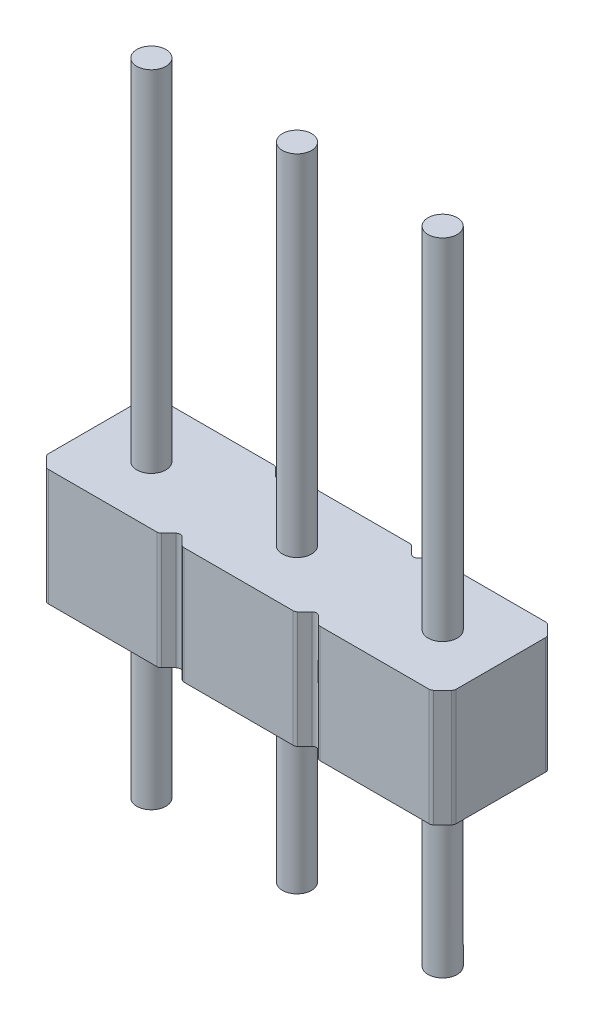
SolidWorks part; units mm, degrees
ref_plane "Ön Düzlem" through (0, 0, 0) normal (0, 0, 1) x (1, 0, 0)
ref_plane "Üst Düzlem" through (0, 0, 0) normal (0, 1, 0) x (1, 0, 0)
ref_plane "Sağ Düzlem" through (0, 0, 0) normal (1, 0, 0) x (0, 0, -1)
sketch "Çizim1" plane through (0, 0, 0) normal (0, 1, 0) x (1, 0, 0)
  line L0 (-3.5, 0) -> (0, 0) construction
  line L1 (0, 0) -> (0, 1) construction
  line L2 (-3.4777, 0.8223) -> (-3.3223, 0.9777)
  line L3 (-3.2684, -1) -> (-1.4016, -1)
  line L4 (-3.5, -0.7684) -> (-3.5, 0.7684)
  line L5 (-3.2684, 1) -> (-1.4016, 1)
  line L6 (3.5, -0.7684) -> (3.5, 0.7684)
  line L7 (-3.5, -1) -> (3.5, 1) construction
  line L8 (-3.5, 1) -> (3.5, -1) construction
  line L9 (-3.4777, -0.8223) -> (-3.3223, -0.9777)
  line L10 (3.3223, 0.9777) -> (3.4777, 0.8223)
  line L11 (3.3223, -0.9777) -> (3.4777, -0.8223)
  line L14 (-3.5, 0.8) -> (3.5, 0.8) construction
  line L15 (-3.5, -0.8) -> (3.5, -0.8) construction
  line L17 (-1.224, -0.854) -> (-1.3477, -0.9777)
  line L18 (-1.224, 0.854) -> (-1.3477, 0.9777)
  line L19 (-1.116, 0.854) -> (-0.9923, 0.9777)
  line L20 (-0.9384, 1) -> (0.9351, 1)
  line L21 (-1.116, -0.854) -> (-0.9923, -0.9777)
  line L22 (-0.9384, -1) -> (0.9351, -1)
  line L23 (1.1127, 0.854) -> (0.989, 0.9777)
  line L24 (1.2206, 0.854) -> (1.3443, 0.9777)
  line L26 (1.1127, -0.854) -> (0.989, -0.9777)
  line L27 (1.2206, -0.854) -> (1.3443, -0.9777)
  line L28 (1.3983, -1) -> (3.2684, -1)
  line L29 (1.3983, 1) -> (3.2684, 1)
  circle A0 centre (0, 0) radius 0.25
  arc A3 (-3.4777, -0.8223) -> (-3.5, -0.7684) centre (-3.4237, -0.7684) cw
  arc A4 (-3.3223, -0.9777) -> (-3.2684, -1) centre (-3.2684, -0.9237) ccw
  arc A5 (-1.3477, -0.9777) -> (-1.4016, -1) centre (-1.4016, -0.9237) cw
  arc A6 (-1.116, -0.854) -> (-1.224, -0.854) centre (-1.17, -0.9079) ccw
  arc A7 (-0.9923, -0.9777) -> (-0.9384, -1) centre (-0.9384, -0.9237) ccw
  arc A8 (0.989, -0.9777) -> (0.9351, -1) centre (0.9351, -0.9237) cw
  arc A9 (1.2206, -0.854) -> (1.1127, -0.854) centre (1.1667, -0.9079) ccw
  arc A10 (1.3443, -0.9777) -> (1.3983, -1) centre (1.3983, -0.9237) ccw
  arc A11 (3.3223, -0.9777) -> (3.2684, -1) centre (3.2684, -0.9237) cw
  arc A12 (3.4777, -0.8223) -> (3.5, -0.7684) centre (3.4237, -0.7684) ccw
  arc A13 (3.4777, 0.8223) -> (3.5, 0.7684) centre (3.4237, 0.7684) cw
  arc A14 (3.3223, 0.9777) -> (3.2684, 1) centre (3.2684, 0.9237) ccw
  arc A15 (1.3443, 0.9777) -> (1.3983, 1) centre (1.3983, 0.9237) cw
  arc A16 (1.1127, 0.854) -> (1.2206, 0.854) centre (1.1667, 0.9079) ccw
  arc A17 (0.989, 0.9777) -> (0.9351, 1) centre (0.9351, 0.9237) ccw
  arc A18 (-0.9923, 0.9777) -> (-0.9384, 1) centre (-0.9384, 0.9237) cw
  arc A19 (-1.116, 0.854) -> (-1.224, 0.854) centre (-1.17, 0.9079) cw
  arc A20 (-1.3477, 0.9777) -> (-1.4016, 1) centre (-1.4016, 0.9237) ccw
  arc A21 (-3.4777, 0.8223) -> (-3.5, 0.7684) centre (-3.4237, 0.7684) ccw
  arc A22 (-3.3223, 0.9777) -> (-3.2684, 1) centre (-3.2684, 0.9237) cw
  circle A23 centre (-2.5, 0) radius 0.25
  circle A24 centre (2.5, 0) radius 0.25
  point P39 (-3.3, -1)
  point P44 (-1.17, -0.8)
  point P47 (-0.97, -1)
  point P52 (1.1667, -0.8)
  point P55 (1.3667, -1)
  point P58 (3.3, -1)
  point P67 (3.3, 1)
  point P70 (1.3667, 1)
  point P73 (1.1667, 0.8)
  point P78 (-0.97, 1)
  point P81 (-1.17, 0.8)
  point P89 (-3.3, 1)
  dimension "D2" = 0.5
  dimension "D3" = 2.5
  dimension "D4" = 2.5
  dimension "D8" = 0.0763
  dimension "D9" = 0.5
  dimension "D14" = 0.5
  dimension "D1" = 3.5
  dimension "D5" = 1
  dimension "D6" = 2
  dimension "D7" = 7
extrude "Yükseklik-Ekstrüzyon1" add sketch "Çizim1" along normal blind 2
sketch "Çizim3" plane through (0, 2, 0) normal (0, 1, 0) x (1, 0, 0)
  circle A0 centre (-2.5, 0) radius 0.25
  circle A1 centre (0, 0) radius 0.25
  circle A2 centre (2.5, 0) radius 0.25
extrude "Yükseklik-Ekstrüzyon3" add sketch "Çizim3" along normal blind 6 and the other way blind 5
